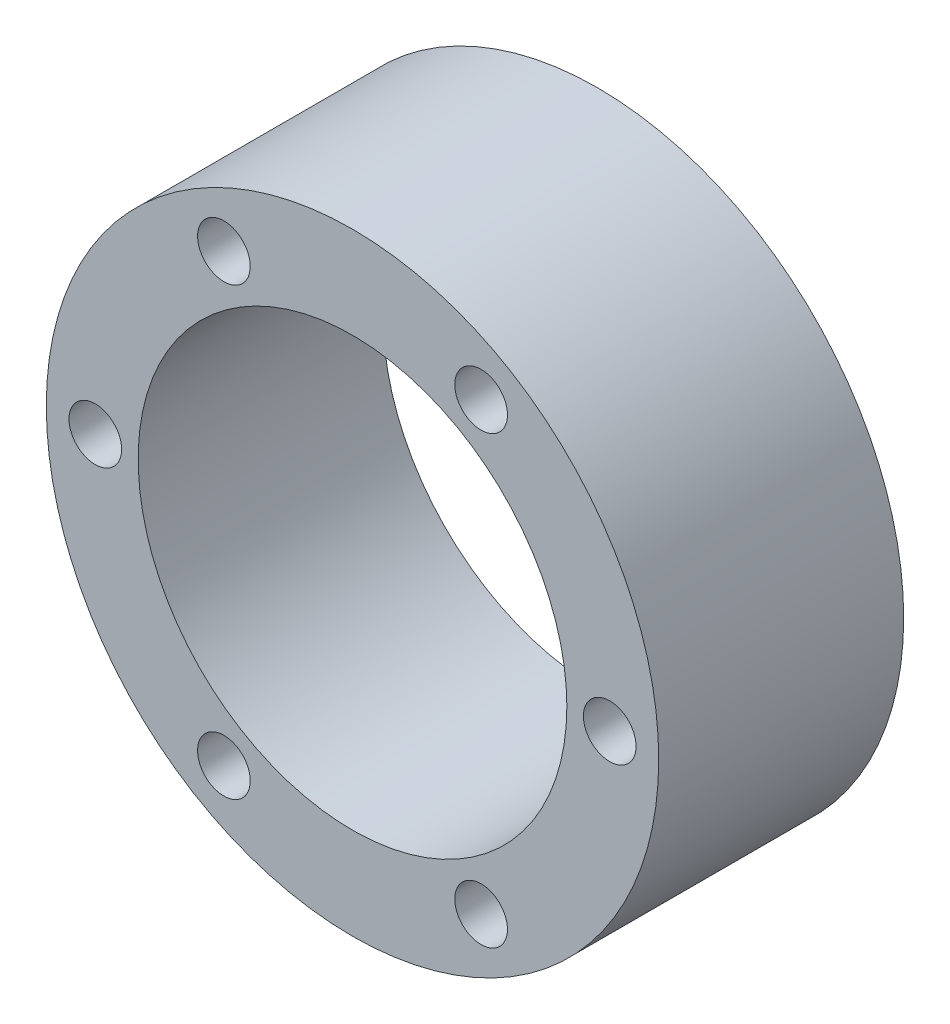
SolidWorks part; units mm, degrees
ref_plane "Alzado" through (0, 0, 0) normal (0, 0, 1) x (1, 0, 0)
ref_plane "Planta" through (0, 0, 0) normal (0, 1, 0) x (1, 0, 0)
ref_plane "Vista lateral" through (0, 0, 0) normal (1, 0, 0) x (0, 0, -1)
sketch "Croquis1" plane through (0, 0, 0) normal (0, 0, 1) x (1, 0, 0)
  circle A0 centre (0, 0) radius 17.5
  circle A1 centre (0, 0) radius 25
  dimension "D1" = 35
  dimension "D2" = 50
extrude "Saliente-Extruir1" add sketch "Croquis1" along normal blind 20
hole_wizard "Taladro de margen para M41" positions "Croquis2" profile "Croquis3" hole size "M4" standard "ISO" end condition through all
sketch "Croquis2" plane through (0, 0, 20) normal (0, 0, 1) x (1, 0, 0)
  point P0 (21, 0)
  point P11 (10.5, -18.1865)
  point P12 (-10.5, -18.1865)
  point P13 (-21, 0)
  point P14 (-10.5, 18.1865)
  point P15 (10.5, 18.1865)
  dimension "D1" = 21
  dimension "D2" = 6
sketch "Croquis3" plane through (21, 0, 20) normal (1, 0, 0) x (0, -1, 0)
  line L0 (0, 0) -> (0, 20)
  line L1 (0, 20) -> (2.15, 20)
  line L2 (2.15, 20) -> (2.15, 0)
  line L5 (2.15, 0) -> (0, 0)
  line L11 (0, -6.35) -> (0, 107.95) construction
  dimension "Diámetro de taladro hasta el siguiente" = 4.3
  dimension "Profundidad de taladro hasta el siguiente" = 20
